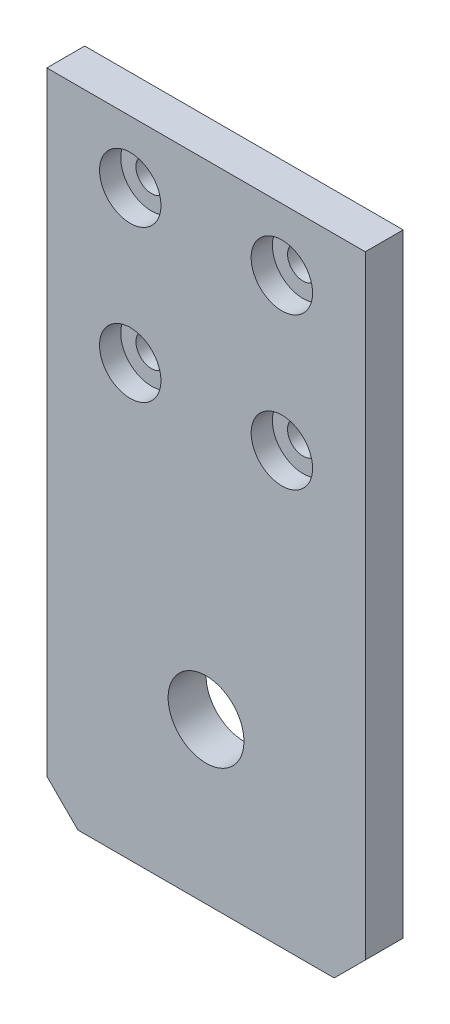
SolidWorks part; units mm, degrees
ref_plane "Alzado" through (0, 0, 0) normal (0, 0, 1) x (1, 0, 0)
ref_plane "Planta" through (0, 0, 0) normal (0, 1, 0) x (1, 0, 0)
ref_plane "Vista lateral" through (0, 0, 0) normal (1, 0, 0) x (0, 0, -1)
sketch "Croquis1" plane through (0, 0, 0) normal (0, 0, 1) x (1, 0, 0)
  line L0 (11, 56.8) -> (31, 76.8) construction
  line L1 (0, 85) -> (42, 85)
  line L2 (0, 85) -> (0, 0)
  line L3 (0, 0) -> (42, 0)
  line L4 (42, 85) -> (42, 0)
  line L5 (21, 66.8) -> (21, 85) construction
  circle A0 centre (11, 76.8) radius 2.05
  circle A1 centre (31, 76.8) radius 2.05
  circle A4 centre (31, 56.8) radius 2.05
  circle A5 centre (11, 56.8) radius 2.05
  dimension "D3" = 4.1
  dimension "D1" = 42
  dimension "D2" = 85
  dimension "D4" = 20
  dimension "D6" = 8.2
  dimension "D7" = 20
extrude "Saliente-Extruir1" add sketch "Croquis1" along normal blind 5
sketch "Croquis4" plane through (0, 0, 5) normal (0, 0, 1) x (1, 0, 0)
  circle A0 centre (11, 76.8) radius 4.05
  circle A1 centre (11, 56.8) radius 4.05
  circle A2 centre (31, 56.8) radius 4.05
  circle A3 centre (31, 76.8) radius 4.05
  dimension "D1" = 8.1
extrude "Cortar-Extruir1" cut sketch "Croquis4" against normal blind 2.8
sketch "Croquis5" plane through (0, 0, 5) normal (0, 0, 1) x (1, 0, 0)
  line L0 (5.5, 36.58) -> (36.5, 5.58) construction
  line L1 (0, 85) -> (42, 85) construction
  line L2 (36.5, 36.58) -> (5.5, 5.58) construction
  line L3 (21, 21.08) -> (21, 0) construction
  line L4 (0, 0) -> (42, 0) construction
  circle A0 centre (21, 21.08) radius 11.5 construction
  circle A1 centre (5.5, 36.58) radius 1.575
  circle A2 centre (36.5, 36.58) radius 1.575
  circle A3 centre (36.5, 5.58) radius 1.575
  circle A4 centre (5.5, 5.58) radius 1.575
  dimension "D1" = 23
  dimension "D4" = 3.15
  dimension "D2" = 31
  dimension "D3" = 31
  dimension "D5" = 63.92
extrude "Cortar-Extruir2" [suppressed] cut sketch "Croquis5" against normal through all
sketch "Croquis6" [suppressed] plane through (0, 0, 5) normal (0, 0, 1) x (1, 0, 0)
  circle A0 centre (5.5, 36.58) radius 3
  circle A1 centre (36.5, 36.58) radius 3
  circle A2 centre (36.5, 5.58) radius 3
  circle A4 centre (5.5, 5.58) radius 3
  dimension "D1" = 6
extrude "Cortar-Extruir3" [suppressed] cut sketch "Croquis6" against normal blind 2.5
chamfer "Chaflán1" distance 4.1 angle 45 2 edges at (42, 0, 2.5) (0, 0, 2.5)
sketch "Croquis7" plane through (0, 0, 5) normal (0, 0, 1) x (1, 0, 0)
  line L0 (5.5, 36.58) -> (36.5, 5.58) construction
  circle A0 centre (21, 21.08) radius 5
  dimension "D1" = 10
extrude "Cortar-Extruir4" cut sketch "Croquis7" against normal through all
